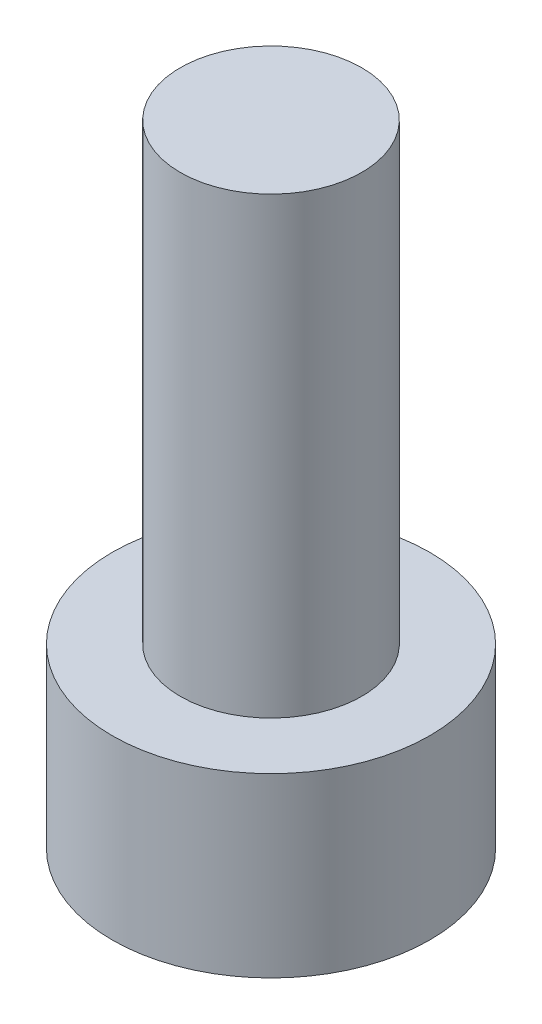
SolidWorks part; units mm, degrees
ref_plane "前视基准面" through (0, 0, 0) normal (0, 0, 1) x (1, 0, 0)
ref_plane "上视基准面" through (0, 0, 0) normal (0, 1, 0) x (1, 0, 0)
ref_plane "右视基准面" through (0, 0, 0) normal (1, 0, 0) x (0, 0, -1)
sketch "草图1" plane through (0, 0, 0) normal (0, 1, 0) x (1, 0, 0)
  circle A0 centre (0, 0) radius 3.5
extrude "凸台-拉伸1" add sketch "草图1" along normal blind 3.9
sketch "草图2" plane through (0, 3.9, 0) normal (0, 1, 0) x (1, 0, 0)
  circle A0 centre (0, 0) radius 2
extrude "凸台-拉伸2" add sketch "草图2" along normal blind 10
sketch "草图3" plane through (0, 0, 0) normal (0, -1, 0) x (1, 0, 0)
  line L1 (1.725, 0) -> (0.8625, 1.4939)
  line L2 (0.8625, 1.4939) -> (-0.8625, 1.4939)
  line L3 (-0.8625, 1.4939) -> (-1.725, 0)
  line L4 (-1.725, 0) -> (-0.8625, -1.4939)
  line L5 (-0.8625, -1.4939) -> (0.8625, -1.4939)
  line L6 (0.8625, -1.4939) -> (1.725, 0)
  circle A0 centre (0, 0) radius 1.4939 construction
extrude "切除-拉伸1" cut sketch "草图3" against normal blind 2.4
